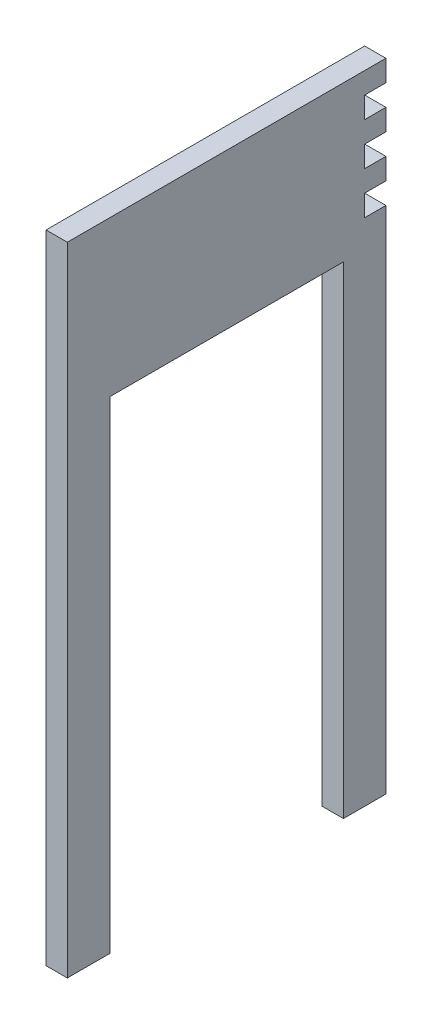
SolidWorks part; units mm, degrees
ref_plane "Plan de face" through (0, 0, 0) normal (0, 0, 1) x (1, 0, 0)
ref_plane "Plan de dessus" through (0, 0, 0) normal (0, 1, 0) x (1, 0, 0)
ref_plane "Plan de droite" through (0, 0, 0) normal (1, 0, 0) x (0, 0, -1)
sketch "Esquisse1" plane through (0, 0, 0) normal (1, 0, 0) x (0, 0, -1)
  line L0 (0, -300) -> (-20, -300)
  line L1 (0, 0) -> (-150, 0)
  line L2 (0, 0) -> (0, -300)
  line L3 (-20, -300) -> (-20, -73)
  line L4 (-150, 0) -> (-150, -300)
  line L5 (-20, -73) -> (-130, -73)
  line L6 (-130, -73) -> (-130, -300)
  line L7 (-130, -300) -> (-150, -300)
  dimension "D1" = 300
  dimension "D2" = 150
  dimension "D3" = 73
  dimension "D4" = 20
  dimension "D5" = 20
  dimension "D6" = 300
extrude "Boss.-Extru.1" add sketch "Esquisse1" along normal blind 10
sketch "Esquisse2" plane through (10, 0, 0) normal (1, 0, 0) x (0, 0, -1)
  line L0 (0, -300) -> (0, 0) construction
  line L1 (0, -10) -> (-10, -10)
  line L2 (0, -10) -> (0, -20)
  line L3 (0, -20) -> (-10, -20)
  line L4 (-10, -10) -> (-10, -20)
  line L5 (0, 0) -> (-150, 0) construction
  dimension "D1" = 10
  dimension "D2" = 10
  dimension "D3" = 10
extrude "Enlèv. mat.-Extru.1" cut sketch "Esquisse2" against normal blind 10
pattern_linear "Répétition linéaire1" count 3 spacing 20 along (0, -1, 0) of "Enlèv. mat.-Extru.1"
